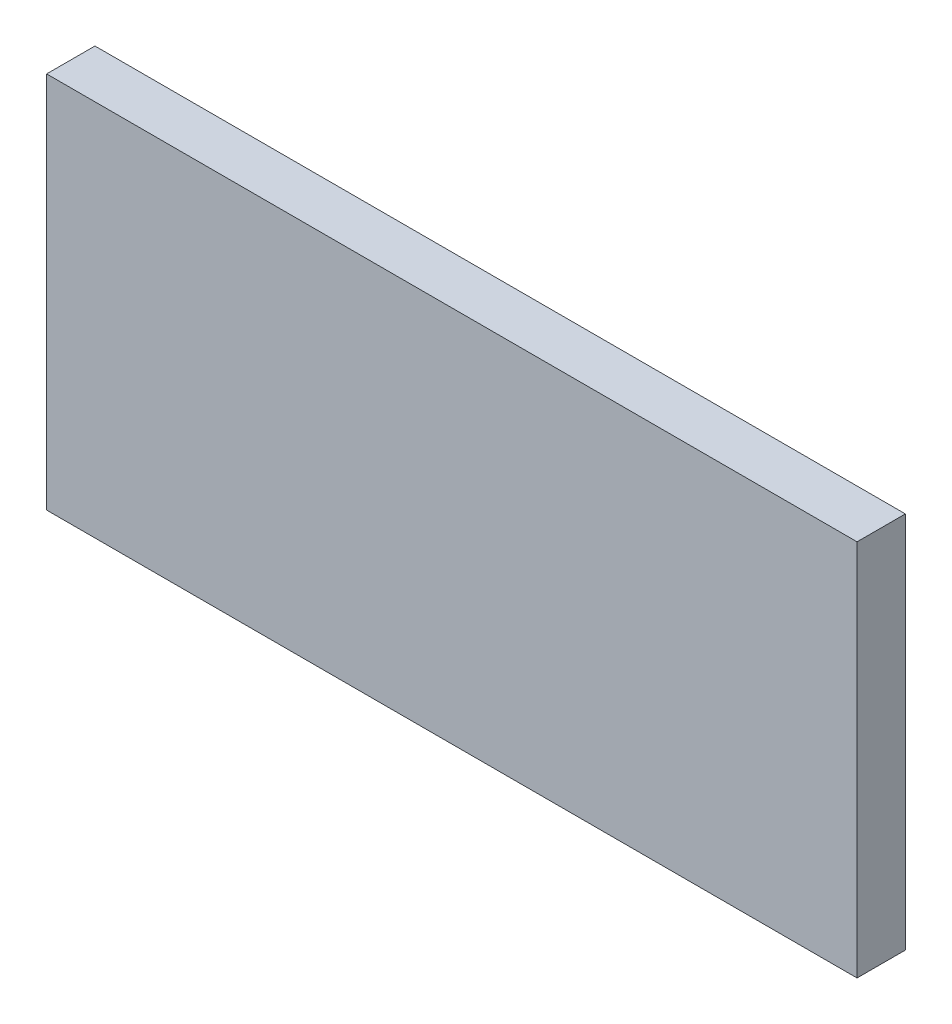
SolidWorks part; units mm, degrees
ref_plane "Plan de face" through (0, 0, 0) normal (0, 0, 1) x (1, 0, 0)
ref_plane "Plan de dessus" through (0, 0, 0) normal (0, 1, 0) x (1, 0, 0)
ref_plane "Plan de droite" through (0, 0, 0) normal (1, 0, 0) x (0, 0, -1)
sketch "Esquisse1" plane through (0, 0, 0) normal (0, 0, 1) x (1, 0, 0)
  line L1 (-184.5, 86) -> (184.5, 86)
  line L2 (-184.5, 86) -> (-184.5, -86)
  line L3 (-184.5, -86) -> (184.5, -86)
  line L4 (184.5, 86) -> (184.5, -86)
  line L5 (-184.5, 86) -> (184.5, -86) construction
  line L6 (-184.5, -86) -> (184.5, 86) construction
  point P0 (0, 0)
  dimension "D1" = 369
  dimension "D2" = 172
extrude "Boss.-Extru.1" add sketch "Esquisse1" along normal blind 22
